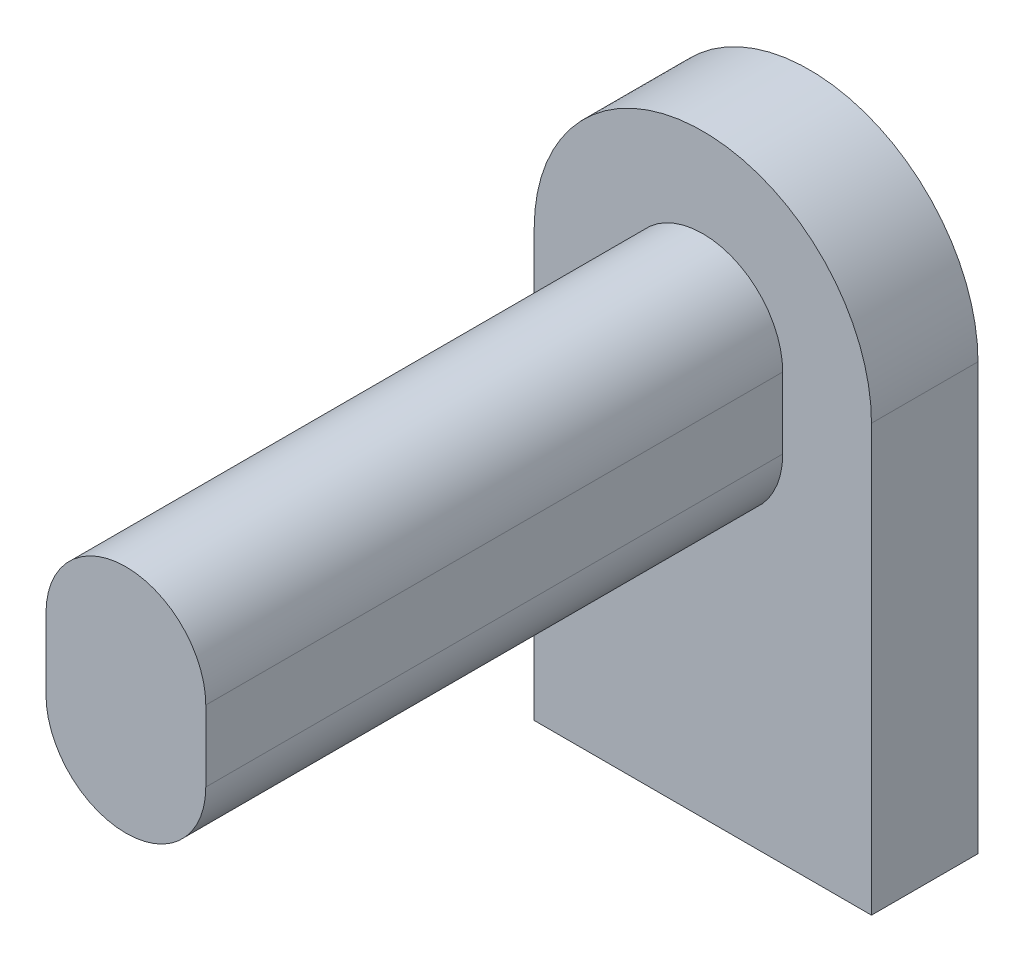
SolidWorks part; units mm, degrees
ref_plane "Front" through (0, 0, 0) normal (0, 0, 1) x (1, 0, 0)
ref_plane "Top" through (0, 0, 0) normal (0, 1, 0) x (1, 0, 0)
ref_plane "Right" through (0, 0, 0) normal (1, 0, 0) x (0, 0, -1)
sketch "Sketch1" plane through (0, 0, 0) normal (0, 0, 1) x (1, 0, 0)
  line L0 (-54.7352, 20.8584) -> (-54.7352, 20.0584)
  line L1 (-52.9352, 20.8584) -> (-52.9352, 20.0584)
  arc A0 (-54.7352, 20.8584) -> (-52.9352, 20.8584) centre (-53.8352, 20.8584) cw
  arc A1 (-52.9352, 20.0584) -> (-54.7352, 20.0584) centre (-53.8352, 20.0584) cw
extrude "Boss-Extrude1" add sketch "Sketch1" along normal blind 6.5
sketch "Sketch3" plane through (0, 0, 0) normal (0, 0, -1) x (-1, 0, 0)
  line L0 (51.9352, 20.8584) -> (55.7352, 20.8584) construction
  line L1 (51.9352, 20.8584) -> (51.9352, 16.0584)
  line L2 (55.7352, 20.8584) -> (55.7352, 16.0584)
  line L3 (51.9352, 16.0584) -> (55.7352, 16.0584)
  arc A0 (51.9352, 20.8584) -> (55.7352, 20.8584) centre (53.8352, 20.8584) cw
  point P4 (53.8352, 20.8584)
  arc M5 (54.7352, 20.8584) -> (52.9352, 20.8584) centre (53.8352, 20.8584) ccw
  line M6 (52.9352, 20.8584) -> (52.9352, 20.0584)
  arc M7 (52.9352, 20.0584) -> (54.7352, 20.0584) centre (53.8352, 20.0584) ccw
  line M8 (54.7352, 20.0584) -> (54.7352, 20.8584)
extrude "Boss-Extrude2" add sketch "Sketch3" along normal blind 1.2 contours L0 L1 L3 L2 M8 M7 M6 | A0 L0 M5 | L0 M6 M7 M8 | L0 M5
